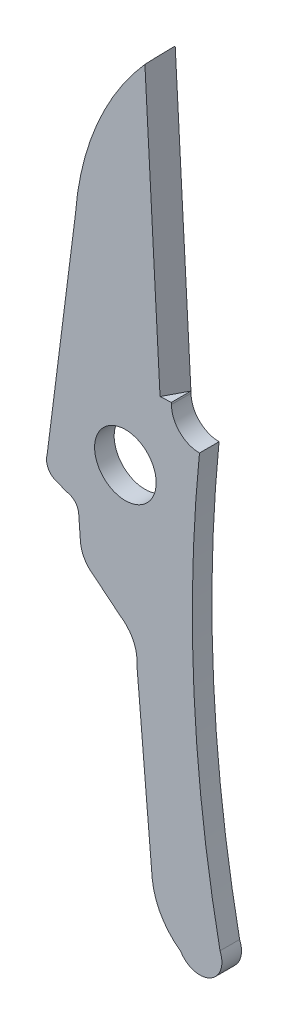
SolidWorks part; units mm, degrees
material "AISI 4340 Steel, normalized"
ref_plane "Front Plane" through (0, 0, 0) normal (0, 0, 1) x (1, 0, 0)
ref_plane "Top Plane" through (0, 0, 0) normal (0, 1, 0) x (1, 0, 0)
ref_plane "Right Plane" through (0, 0, 0) normal (1, 0, 0) x (0, 0, -1)
sketch "Sketch1" plane through (0, 0, 0) normal (0, 0, 1) x (1, 0, 0)
  line L0 (-34.2684, 6.7209) -> (42.5577, -21.2415) construction
  line L1 (8.8754, 21.3967) -> (9.5935, 8.1175)
  line L2 (8.0276, -2.912) -> (8.7218, -10.9498)
  line L3 (6.0654, -0.3642) -> (7.2579, -1.3383)
  line L4 (5.3889, 1.6796) -> (5.4618, 0.716)
  line L5 (4.4198, 2.4702) -> (4.8683, 2.3033)
  line L6 (5.2417, 13.4498) -> (3.9519, 3.3124)
  arc A0 (9.5935, 8.1175) -> (10.8647, 6.8463) centre (10.8647, 8.1175) ccw
  arc A1 (10.8647, 6.8463) -> (11.7972, -12.2447) centre (74.7935, 0.4005) ccw
  arc A2 (11.7972, -12.2447) -> (10.0144, -13.1581) centre (10.8801, -12.6513) cw
  arc A3 (10.0144, -13.1581) -> (8.7218, -10.9498) centre (11.8018, -10.6295) cw
  arc A4 (8.0276, -2.912) -> (7.2579, -1.3383) centre (6.3351, -2.7647) ccw
  arc A5 (5.4618, 0.716) -> (6.0654, -0.3642) centre (6.8334, 0.7737) ccw
  arc A6 (4.8683, 2.3033) -> (5.3889, 1.6796) centre (4.7549, 1.6796) cw
  arc A7 (3.9519, 3.3124) -> (4.4198, 2.4702) centre (4.607, 3.1252) ccw
  arc A8 (8.8754, 21.3967) -> (5.2417, 13.4498) centre (17.9, 12.466) ccw
  circle A9 centre (7.504, 4.6908) radius 1.397
  dimension "D1" = 2.794
  dimension "D3" = 12.6965
  dimension "D5" = 0.6812
  dimension "D6" = 0.634
  dimension "D9" = 1.3728
  dimension "D12" = 64.2529
  dimension "D13" = 1.0031
  dimension "D14" = 3.0966
  dimension "D15" = 1.2713
  dimension "D2" = 13.2792
  dimension "D4" = 10.1374
  dimension "D7" = 0.4786
  dimension "D8" = 0.9635
  dimension "D10" = 0.9741
  dimension "D11" = 8.0377
extrude "Boss-Extrude1" add sketch "Sketch1" along normal mid plane 0.889
ref_plane "Plane1" through (-1.3056, 24.1425, 0) normal (-0.054, 0.9985, 0) x (0.9985, 0.054, 0)
sketch "Sketch2" plane through (-1.3056, 24.1425, 0) normal (-0.054, 0.9985, 0) x (0.9985, 0.054, 0)
  line L0 (10.0178, 0.4445) -> (10.0178, -0.4445)
  line L1 (10.0178, -0.4445) -> (9.5045, -0.4445)
  line L2 (9.5045, -0.4445) -> (10.0178, 0.4445)
  point P2 (0, 0)
  point P4 (0, 0)
  point P5 (0, 0)
  point P7 (0, 0)
  point P8 (0, 0)
  dimension "D1" = 30
extrude "Cut-Extrude4" cut sketch "Sketch2" against normal blind 16.51
